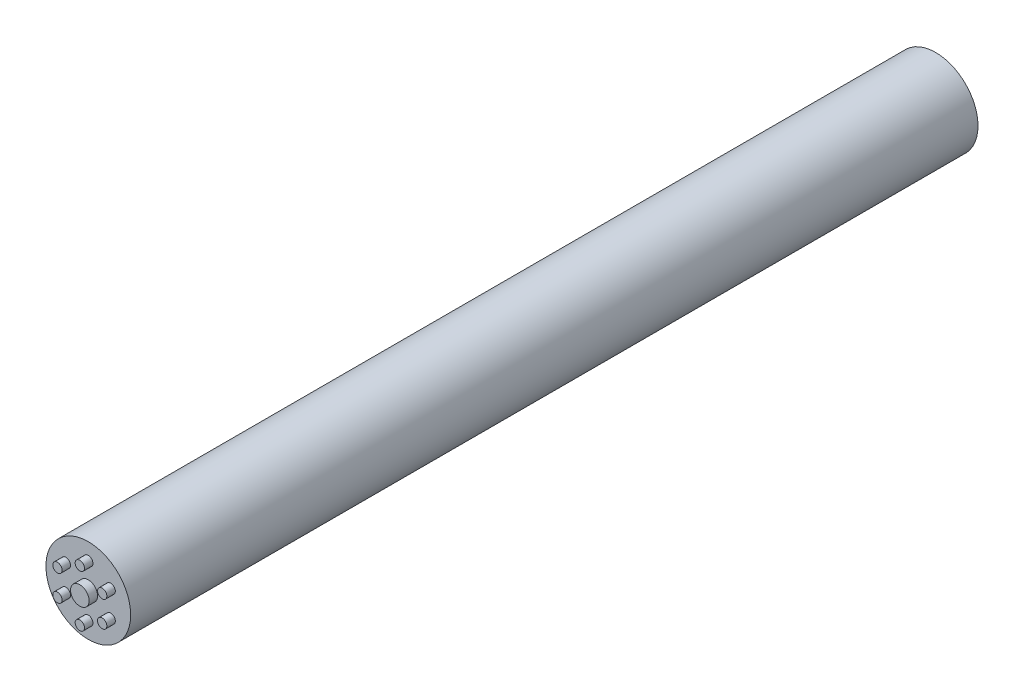
SolidWorks part; units mm, degrees
ref_plane "Front Plane" through (0, 0, 0) normal (0, 0, 1) x (1, 0, 0)
ref_plane "Top Plane" through (0, 0, 0) normal (0, 1, 0) x (1, 0, 0)
ref_plane "Right Plane" through (0, 0, 0) normal (1, 0, 0) x (0, 0, -1)
sketch "Sketch1" plane through (0, 0, 0) normal (0, 0, 1) x (1, 0, 0)
  circle A0 centre (0, 0) radius 5
extrude "Boss-Extrude1" add sketch "Sketch1" along normal blind 100
sketch "Sketch3" plane through (0, 0, 100) normal (0, 0, 1) x (1, 0, 0)
  circle A0 centre (0, 0) radius 1.1
  circle A1 centre (-2.6422, 1.5255) radius 0.55
  circle A2 centre (0, 3.051) radius 0.55
  circle A3 centre (-2.6422, -1.5255) radius 0.55
  circle A4 centre (0, -3.051) radius 0.55
  circle A5 centre (2.6422, -1.5255) radius 0.55
  circle A6 centre (2.6422, 1.5255) radius 0.55
extrude "Boss-Extrude3" add sketch "Sketch3" along normal blind 1 contours A0 | A6 | A5 | A4 | A3 | A1 | A2
